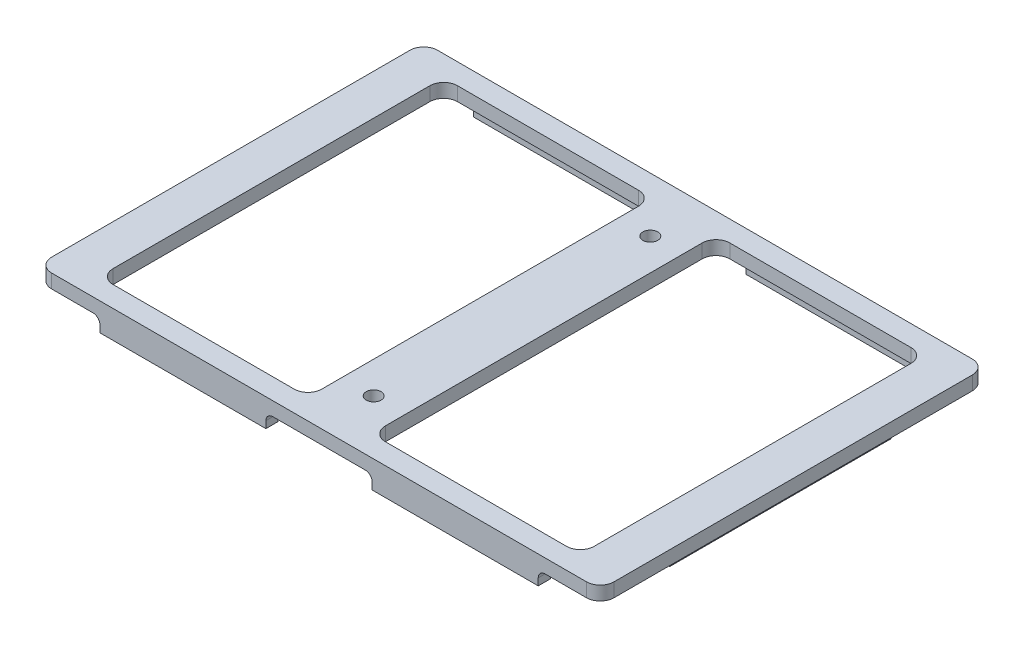
SolidWorks part; units mm, degrees
ref_plane "Front Plane" through (0, 0, 0) normal (0, 0, 1) x (1, 0, 0)
ref_plane "Top Plane" through (0, 0, 0) normal (0, 1, 0) x (1, 0, 0)
ref_plane "Right Plane" through (0, 0, 0) normal (1, 0, 0) x (0, 0, -1)
sketch "Sketch1" plane through (0, 0, 0) normal (0, 1, 0) x (1, 0, 0)
  line L1 (64.5414, -44.2849) -> (-64.5414, -44.2849)
  line L2 (64.5414, -44.2849) -> (64.5414, 44.2849)
  line L3 (64.5414, 44.2849) -> (-64.5414, 44.2849)
  line L4 (-64.5414, -44.2849) -> (-64.5414, 44.2849)
  line L5 (64.5414, -44.2849) -> (-64.5414, 44.2849) construction
  line L6 (64.5414, 44.2849) -> (-64.5414, -44.2849) construction
  point P0 (0, 0)
  dimension "D1" = 88.5698
  dimension "D2" = 129.0828
extrude "Boss-Extrude1" add sketch "Sketch1" along normal blind 3.175
sketch "Sketch3" plane through (0, 0, 0) normal (0, -1, 0) x (1, 0, 0)
  line L0 (-4.1275, -41.1099) -> (-58.3819, -41.1099) construction
  line L1 (-58.3819, -41.1099) -> (-58.3819, 41.1099) construction
  line L2 (-58.3819, 41.1099) -> (-4.1275, 41.1099) construction
  line L3 (-4.1275, 41.1099) -> (-4.1275, -41.1099) construction
  line L4 (58.3819, -41.1099) -> (4.1275, -41.1099) construction
  line L5 (4.1275, -41.1099) -> (4.1275, 41.1099) construction
  line L6 (4.1275, 41.1099) -> (58.3819, 41.1099) construction
  line L7 (58.3819, 41.1099) -> (58.3819, -41.1099) construction
  line L8 (-4.1275, -41.1099) -> (-58.3819, -41.1099) construction
  line L9 (-58.3819, -41.1099) -> (-58.3819, 41.1099) construction
  line L10 (-58.3819, 41.1099) -> (-4.1275, 41.1099) construction
  line L11 (-4.1275, 41.1099) -> (-4.1275, -41.1099) construction
  line L12 (58.3819, -41.1099) -> (4.1275, -41.1099) construction
  line L13 (4.1275, -41.1099) -> (4.1275, 41.1099) construction
  line L14 (4.1275, 41.1099) -> (58.3819, 41.1099) construction
  line L15 (58.3819, 41.1099) -> (58.3819, -41.1099) construction
  line L16 (-31.2547, -41.1099) -> (-31.2547, 41.1099) construction
  line L17 (31.2547, -41.1099) -> (31.2547, 41.1099) construction
  line L19 (-7.3025, 39.5224) -> (-55.2069, 39.5224)
  line L20 (-7.3025, 39.5224) -> (-7.3025, -39.5224)
  line L21 (-7.3025, -39.5224) -> (-55.2069, -39.5224)
  line L22 (-55.2069, 39.5224) -> (-55.2069, -39.5224)
  line L23 (-7.3025, 39.5224) -> (-55.2069, -39.5224) construction
  line L24 (-7.3025, -39.5224) -> (-55.2069, 39.5224) construction
  line L25 (55.2069, 39.5224) -> (7.3025, 39.5224)
  line L26 (55.2069, 39.5224) -> (55.2069, -39.5224)
  line L27 (55.2069, -39.5224) -> (7.3025, -39.5224)
  line L28 (7.3025, 39.5224) -> (7.3025, -39.5224)
  line L29 (55.2069, 39.5224) -> (7.3025, -39.5224) construction
  line L30 (55.2069, -39.5224) -> (7.3025, 39.5224) construction
  point P10 (-31.2547, 0)
  point P17 (31.2547, 0)
  dimension "D1" = 3.175
  dimension "D2" = 3.175
extrude "Cut-Extrude1" cut sketch "Sketch3" against normal through all contours L20 L19 L22 L21 | L26 L25 L28 L27
fillet "Fillet1" radius 3.175 12 edges at (7.3025, 1.5875, 39.5224) (55.2069, 1.5875, 39.5224) (55.2069, 1.5875, -39.5224) (7.3025, 1.5875, -39.5224) (-55.2069, 1.5875, 39.5224) (-7.3025, 1.5875, 39.5224) (-55.2069, 1.5875, -39.5224) (-7.3025, 1.5875, -39.5224) (64.5414, 1.5875, -44.2849) (64.5414, 1.5875, 44.2849) (-64.5414, 1.5875, 44.2849) (-64.5414, 1.5875, -44.2849)
sketch "Sketch5" plane through (0, 0, 0) normal (0, -1, 0) x (1, 0, 0)
  line L0 (-4.1275, -41.1099) -> (-58.3819, -41.1099) construction
  line L1 (-50.3047, 44.2849) -> (-12.2047, 44.2849)
  line L2 (-50.3047, 44.2849) -> (-50.3047, 41.4909)
  line L3 (-50.3047, 41.4909) -> (-12.2047, 41.4909)
  line L4 (-12.2047, 44.2849) -> (-12.2047, 41.4909)
  line L5 (-61.5569, 25.4) -> (-58.7629, 25.4)
  line L6 (-61.5569, 25.4) -> (-61.5569, -25.4)
  line L7 (-61.5569, -25.4) -> (-58.7629, -25.4)
  line L8 (-58.7629, 25.4) -> (-58.7629, -25.4)
  line L9 (-50.3047, -41.4909) -> (-12.2047, -41.4909)
  line L10 (-50.3047, -41.4909) -> (-50.3047, -44.2849)
  line L11 (-50.3047, -44.2849) -> (-12.2047, -44.2849)
  line L12 (-12.2047, -41.4909) -> (-12.2047, -44.2849)
  line L13 (-58.3819, 41.1099) -> (-4.1275, 41.1099) construction
  line L14 (-61.3664, 44.2849) -> (61.3664, 44.2849) construction
  line L15 (-31.2547, 41.4909) -> (-31.2547, 44.2849) construction
  line L16 (-31.2547, -41.1099) -> (-31.2547, 41.1099) construction
  line L17 (61.3664, -44.2849) -> (-61.3664, -44.2849) construction
  line L18 (-58.3819, -41.1099) -> (-58.3819, 41.1099) construction
  line L19 (-58.3819, 0) -> (-31.2547, 0) construction
  point P22 (-31.2547, -41.4909)
  point P30 (-58.7629, 0)
  dimension "D1" = 0.381
  dimension "D2" = 0.381
  dimension "D3" = 38.1
  dimension "D4" = 0.381
  dimension "D5" = 50.8
extrude "Boss-Extrude2" add sketch "Sketch5" along normal blind 3.175
fillet "Fillet2" radius 1.5875 7 edges at (-61.5569, 0, 0) (-60.1599, 0, -25.4) (-60.1599, 0, 25.4) (-12.2047, 0, 42.8879) (-50.3047, 0, 42.8879) (-50.3047, 0, -42.8879) (-12.2047, 0, -42.8879)
mirror "Mirror1" about plane through (0, 0, 0) normal (1, 0, 0) of "Fillet2", "Boss-Extrude2"
sketch "Sketch6" plane through (0, 3.175, 0) normal (0, 1, 0) x (1, 0, 0)
  line L8 (3.8735, 41.1132) -> (-3.8735, 41.1132)
  line L9 (-3.8735, 41.1132) -> (-3.8735, -41.1132)
  line L10 (-3.8735, -41.1132) -> (3.8735, -41.1132)
  line L11 (3.8735, -41.1132) -> (3.8735, 41.1132)
  line L12 (3.8735, 41.1132) -> (-3.8735, 41.1132)
  line L13 (-3.8735, 41.1132) -> (-3.8735, -41.1132)
  line L14 (-3.8735, -41.1132) -> (3.8735, -41.1132)
  line L15 (3.8735, -41.1132) -> (3.8735, 41.1132)
  dimension "D1" = 0
hole_wizard "M3 Clearance Hole1" positions "Sketch7" profile "Sketch8" hole size "M3" standard "ANSI Metric" end condition through all
sketch "Sketch7" plane through (0, 3.175, 0) normal (0, 1, 0) x (1, 0, 0)
  line L0 (0, 31.75) -> (0, -31.75) construction
  point P1 (0, 31.75)
  point P2 (0, -31.75)
  point P4 (0, 0)
  dimension "D1" = 63.5
sketch "Sketch8" plane through (0, 3.175, -31.75) normal (1, 0, 0) x (0, 0, 1)
  line L0 (0, 0) -> (0, 6.35)
  line L1 (0, 6.35) -> (1.7, 6.35)
  line L2 (1.7, 6.35) -> (1.7, 0)
  line L5 (1.7, 0) -> (0, 0)
  line L11 (0, -6.35) -> (0, 107.95) construction
  dimension "Thru Hole Dia." = 3.4
  dimension "Thru Hole Depth" = 6.35
